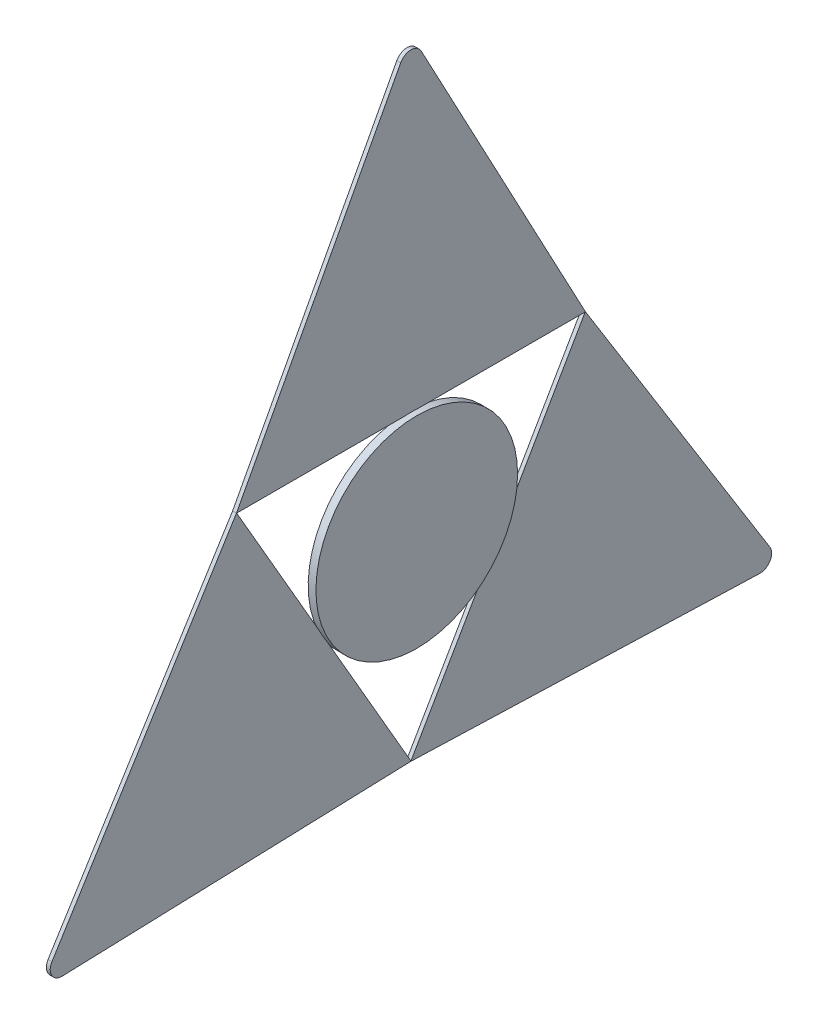
SolidWorks part; units mm, degrees
material "PVC Rigid"
ref_plane "Front Plane" through (0, 0, 0) normal (0, 0, 1) x (1, 0, 0)
ref_plane "Top Plane" through (0, 0, 0) normal (0, 1, 0) x (1, 0, 0)
ref_plane "Right Plane" through (0, 0, 0) normal (1, 0, 0) x (0, 0, -1)
sketch "Sketch1" plane through (0, 0, 0) normal (1, 0, 0) x (0, 0, -1)
  line L0 (-1.3235, 0.7059) -> (-22.5, -39)
  line L1 (-22.5, -39) -> (22.5, -39)
  line L2 (22.5, -39) -> (1.3235, 0.7059)
  arc A0 (-1.3235, 0.7059) -> (1.3235, 0.7059) centre (0, 0) cw
  dimension "D1" = 1.5
  dimension "D2" = 45
extrude "Boss-Extrude1" add sketch "Sketch1" along normal mid plane 0.5 contours L0 L1 L2 A0
sketch "Sketch2" plane through (0, 0, 0) normal (1, 0, 0) x (0, 0, -1)
  line L0 (-22.5, -39) -> (22.5, -39) construction
  line L1 (-22.5, -39) -> (0, -77.9711) construction
  line L2 (0, -77.9711) -> (22.5, -39) construction
  circle A0 centre (0, -51.9711) radius 13
  point P2 (0, -51.6025)
  dimension "D3" = 26
  dimension "D1" = 60
  dimension "D2" = 60
extrude "Boss-Extrude2" add sketch "Sketch2" along normal blind 1
pattern_circular "CirPattern1" count 3 over 360 about axis through (0, -51.9711, 0) along (1, 0, 0) of "Boss-Extrude1"
sketch "Sketch4" plane through (0, 0, 0) normal (-1, 0, 0) x (0, 0, 1)
  line L1 (-5, -46.9711) -> (5, -46.9711)
  line L2 (-5, -46.9711) -> (-5, -56.9711)
  line L3 (-5, -56.9711) -> (5, -56.9711)
  line L4 (5, -46.9711) -> (5, -56.9711)
  line L5 (-5, -46.9711) -> (5, -56.9711) construction
  line L6 (-5, -56.9711) -> (5, -46.9711) construction
  arc A0 (11.6662, -57.707) -> (0.8657, -39) centre (0, -51.9711) ccw construction
  arc A1 (11.6662, -57.707) -> (0.8657, -39) centre (0, -51.9711) ccw construction
  point P0 (0, -51.9711)
  dimension "D1" = 10
extrude "Boss-Extrude3" add sketch "Sketch4" along normal blind 2
equation "\"TRIANGLE_SIDE\"=45"
equation "\"D2@Sketch1\"=\"TRIANGLE_SIDE\""
equation "\"D1@Sketch1\"=\"TRIANGLE_SIDE\"*1/30"
